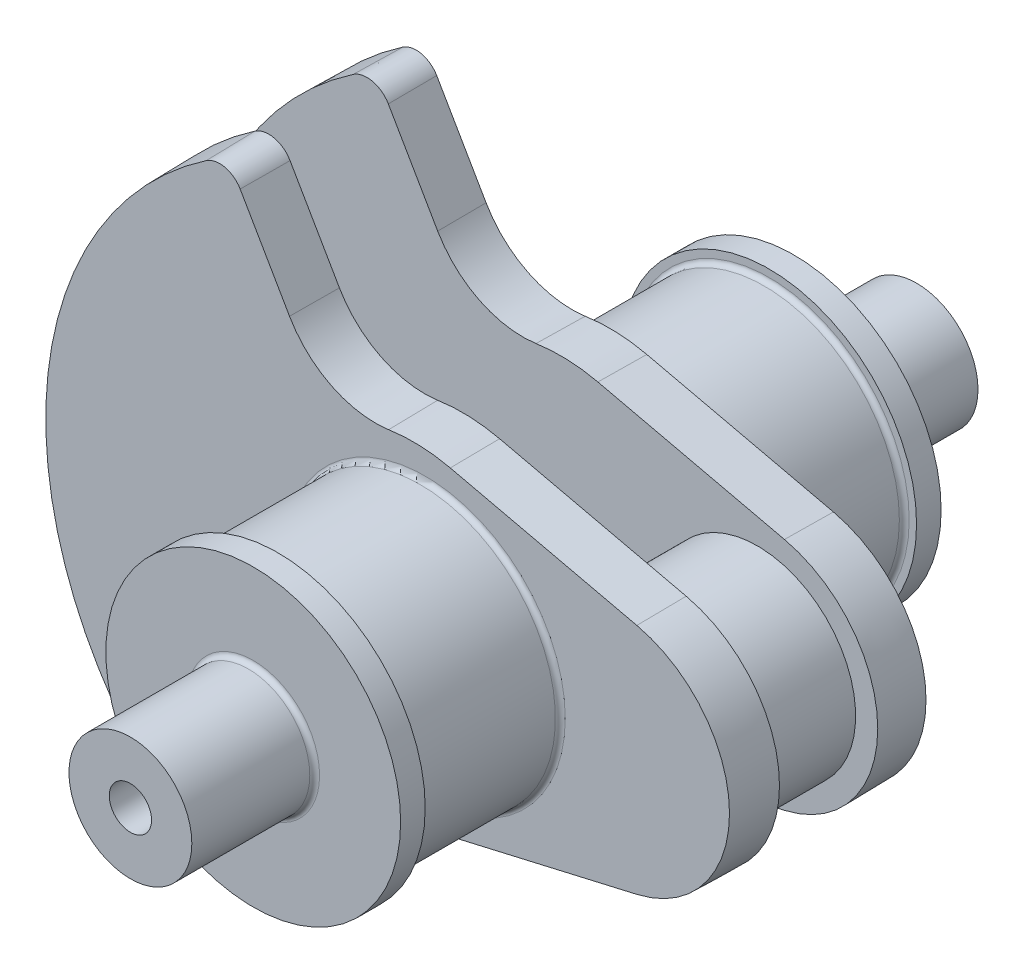
SolidWorks part; units mm, degrees
ref_plane "Front Plane" through (0, 0, 0) normal (0, 0, 1) x (1, 0, 0)
ref_plane "Top Plane" through (0, 0, 0) normal (0, 1, 0) x (1, 0, 0)
ref_plane "Right Plane" through (0, 0, 0) normal (1, 0, 0) x (0, 0, -1)
sketch "Sketch1" plane through (0, 0, 0) normal (0, 0, 1) x (1, 0, 0)
  line L0 (-40, 0) -> (-40, 110.483) construction
  line L1 (0, 0) -> (-168.7701, 0) construction
  line L2 (5.5125, 23.8718) -> (-32.4625, 32.641)
  line L3 (5.5125, -23.8718) -> (-32.4625, -32.641)
  line L4 (-65.0632, -42.9348) -> (-75.1079, -60.3329)
  line L5 (-65.0632, 42.9348) -> (-75.1079, 60.3329)
  line L6 (-40, 0) -> (-40, -61.9003) construction
  arc A0 (5.5125, -23.8718) -> (5.5125, 23.8718) centre (0, 0) ccw
  arc A1 (-32.4625, 32.641) -> (-45.0645, 33.115) centre (-40, 0) ccw
  arc A2 (-82.2551, 61.9638) -> (-82.2551, -61.9638) centre (-40, 0) ccw
  arc A3 (-65.0632, -42.9348) -> (-45.0645, -33.115) centre (-47.7427, -52.9348) cw
  arc A4 (-65.0632, 42.9348) -> (-45.0645, 33.115) centre (-47.7427, 52.9348) ccw
  arc A5 (-45.0645, -33.115) -> (-32.4625, -32.641) centre (-40, 0) ccw
  arc A6 (-75.1079, 60.3329) -> (-82.2551, 61.9638) centre (-79.4381, 57.8329) ccw
  arc A7 (-75.1079, -60.3329) -> (-82.2551, -61.9638) centre (-79.4381, -57.8329) cw
  dimension "D1" = 49
  dimension "D3" = 67
  dimension "D6" = 150
  dimension "D7" = 20
  dimension "D10" = 5
  dimension "D11" = 5
  dimension "D2" = 40
  dimension "D4" = 60
  dimension "D5" = 60
  dimension "D8" = 42.9348
  dimension "D9" = 25.0632
extrude "Boss-Extrude1" add sketch "Sketch1" along normal blind 10 draft 1
sketch "Sketch2" plane through (0, 0, 10) normal (0, 0, 1) x (1, 0, 0)
  circle A0 centre (-37.5985, 0) radius 27.5
  dimension "D1" = 55
extrude "Boss-Extrude2" add sketch "Sketch2" along normal blind 30
sketch "Sketch3" plane through (0, 0, 40) normal (0, 0, 1) x (1, 0, 0)
  line L0 (-37.5985, 27.5) -> (-37.5985, 0) construction
  line L1 (-37.5985, 0) -> (-10.0985, 0) construction
  circle A1 centre (-37.5985, 0) radius 27.5 construction
  circle A2 centre (-37.5985, 0) radius 27.5 construction
  circle A3 centre (-37.5985, 0) radius 30
  dimension "D1" = 60
extrude "Boss-Extrude3" add sketch "Sketch3" along normal blind 5
fillet "Fillet1" radius 1 2 edges at (-65.0985, 0, 10) (-10.0985, 0, 40)
sketch "Sketch4" plane through (0, 0, 45) normal (0, 0, 1) x (1, 0, 0)
  line L0 (-37.5985, 30) -> (-37.5985, 0) construction
  line L1 (-37.5985, 0) -> (-7.5985, 0) construction
  circle A0 centre (-37.5985, 0) radius 30 construction
  circle A1 centre (-37.5985, 0) radius 12.5
  dimension "D1" = 25
extrude "Boss-Extrude4" add sketch "Sketch4" along normal blind 25
fillet "Fillet2" radius 1 1 edges at (-25.0985, 0, 45)
sketch "Sketch5" plane through (0, 0, 70) normal (0, 0, 1) x (1, 0, 0)
  circle A0 centre (-37.5985, 0) radius 4.3029
extrude "Cut-Extrude1" cut sketch "Sketch5" against normal blind 12
sketch "Sketch8" plane through (0, 0, 0) normal (0, 0, -1) x (-1, 0, 0)
  circle A0 centre (0, 0) radius 20
  dimension "D1" = 40
extrude "Boss-Extrude6" add sketch "Sketch8" along normal blind 10
sketch "Sketch9" plane through (0, 0, -10) normal (0, 0, -1) x (-1, 0, 0)
  circle A0 centre (0, 0) radius 20
mirror "Mirror7" about plane through (0, 0, -10) normal (0, 0, -1) of bodies 107
